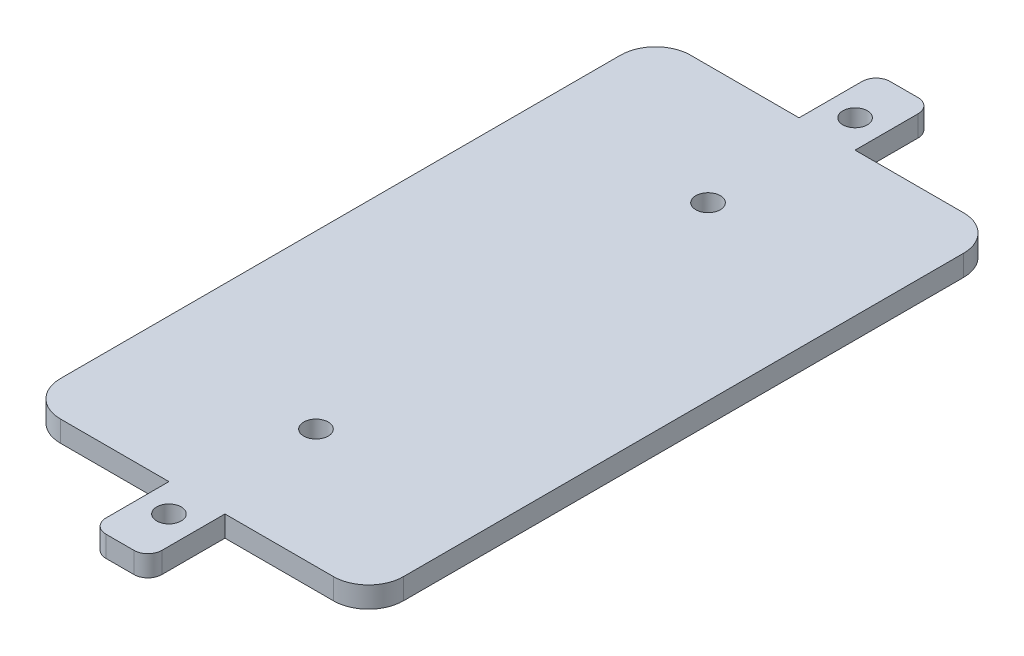
SolidWorks part; units mm, degrees
ref_plane "前视基准面" through (0, 0, 0) normal (0, 0, 1) x (1, 0, 0)
ref_plane "上视基准面" through (0, 0, 0) normal (0, 1, 0) x (1, 0, 0)
ref_plane "右视基准面" through (0, 0, 0) normal (1, 0, 0) x (0, 0, -1)
sketch "草图1" plane through (0, 0, 0) normal (0, 1, 0) x (1, 0, 0)
  line L0 (0, -45) -> (0, -56) construction
  line L1 (-24.5, -45) -> (24.5, -45)
  line L2 (-24.5, -45) -> (-24.5, 45)
  line L3 (-24.5, 45) -> (24.5, 45)
  line L4 (24.5, -45) -> (24.5, 45)
  line L5 (-24.5, -45) -> (24.5, 45) construction
  line L6 (-24.5, 45) -> (24.5, -45) construction
  line L7 (0, -56) -> (4, -56)
  line L8 (4, -56) -> (4, -45)
  line L9 (4, -45) -> (-4, -45)
  line L10 (-4, -45) -> (-4, -56)
  line L11 (-4, -56) -> (0, -56)
  line L12 (0, 0) -> (-24.5, 0) construction
  line L13 (-4, 45) -> (-4, 56)
  line L14 (0, 56) -> (4, 56)
  line L15 (-4, 56) -> (0, 56)
  line L16 (4, 56) -> (4, 45)
  circle A0 centre (0, -49) radius 1.75
  circle A1 centre (0, 49) radius 1.75
  point P0 (0, 0)
  dimension "D6" = 3.5
  dimension "D1" = 49
  dimension "D2" = 90
  dimension "D3" = 11
  dimension "D4" = 4
  dimension "D5" = 4
  dimension "D7" = 4
extrude "凸台-拉伸1" add sketch "草图1" along normal blind 3 contours L1 L4 L3 L2 | L16 L14 L15 L13 L3 A1 | L10 L11 L7 L8 L1 A0
fillet "圆角1" radius 2 4 edges at (4, 1.5, -56) (-4, 1.5, -56) (4, 1.5, 56) (-4, 1.5, 56)
fillet "圆角2" radius 5 4 edges at (-24.5, 1.5, 45) (24.5, 1.5, 45) (24.5, 1.5, -45) (-24.5, 1.5, -45)
sketch "草图2" plane through (0, 0, 0) normal (0, -1, 0) x (1, 0, 0)
  line L0 (0, 49) -> (0, 28)
  line L1 (0, 28) -> (0, -28)
  line L2 (0, -28) -> (0, -49)
  circle A0 centre (0, 28) radius 1.75
  circle A1 centre (0, -28) radius 1.75
  dimension "D2" = 3.5
  dimension "D3" = 3.5
  dimension "D1" = 56
extrude "切除-拉伸1" cut sketch "草图2" against normal blind 10 contours L1 A1 L2 | L2 A1 L1 | L0 A0 L1 | L1 A0 L0
